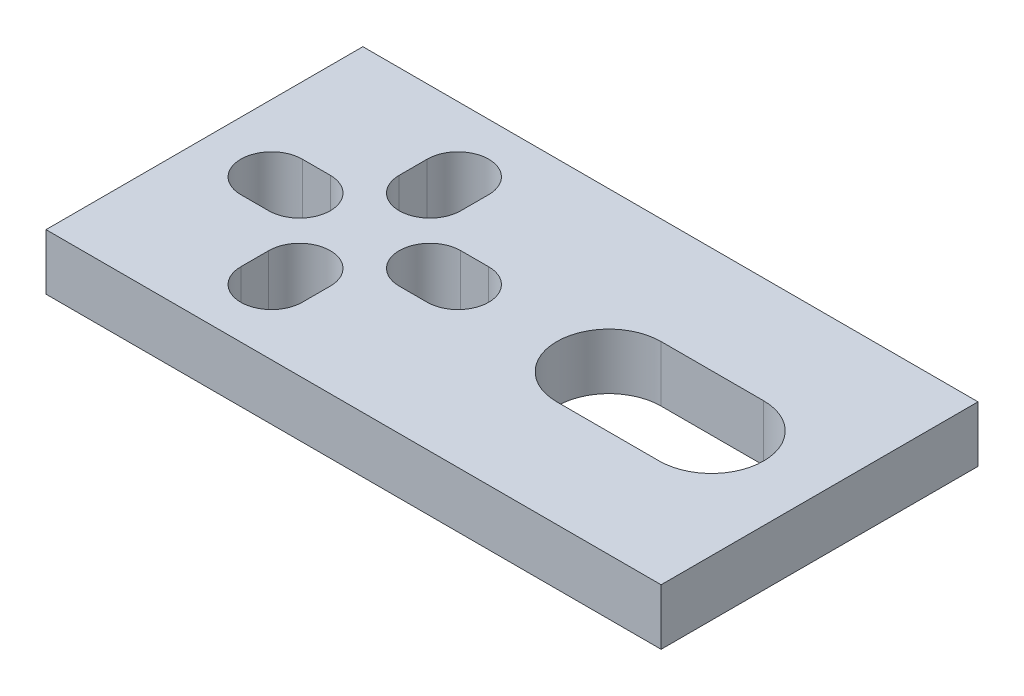
SolidWorks part; units mm, degrees
material "6061-T6 (SS)"
ref_plane "Front Plane" through (0, 0, 0) normal (0, 0, 1) x (1, 0, 0)
ref_plane "Top Plane" through (0, 0, 0) normal (0, 1, 0) x (1, 0, 0)
ref_plane "Right Plane" through (0, 0, 0) normal (1, 0, 0) x (0, 0, -1)
sketch "Sketch1" plane through (0, 0, 0) normal (0, 1, 0) x (1, 0, 0)
  line L1 (0, 0) -> (33, 0)
  line L2 (0, 0) -> (0, 17)
  line L3 (0, 17) -> (33, 17)
  line L4 (33, 0) -> (33, 17)
  dimension "D1" = 33
  dimension "D2" = 17
extrude "Boss-Extrude1" add sketch "Sketch1" along normal blind 3
sketch "Sketch2" plane through (0, 3, 0) normal (0, 1, 0) x (1, 0, 0)
  line L0 (0, 8.5) -> (33, 8.5) construction
  line L1 (0, 17) -> (0, 0) construction
  line L2 (33, 0) -> (33, 17) construction
  line L3 (8.6, 8.5) -> (8.6, 12.75) construction
  line L4 (21.7, 8.5) -> (27.2, 8.5) construction
  line L5 (21.7, 11.3) -> (27.2, 11.3)
  line L6 (21.7, 5.7) -> (27.2, 5.7)
  line L7 (8.6, 12) -> (8.6, 13.5) construction
  line L8 (6.95, 12) -> (6.95, 13.5)
  line L9 (10.25, 12) -> (10.25, 13.5)
  line L10 (3.6, 8.5) -> (5.1, 8.5) construction
  line L11 (3.6, 10.15) -> (5.1, 10.15)
  line L12 (3.6, 6.85) -> (5.1, 6.85)
  line L13 (13.6, 8.5) -> (12.1, 8.5) construction
  line L14 (13.6, 10.15) -> (12.1, 10.15)
  line L15 (13.6, 6.85) -> (12.1, 6.85)
  line L16 (8.6, 5) -> (8.6, 3.5) construction
  line L17 (6.95, 5) -> (6.95, 3.5)
  line L18 (10.25, 5) -> (10.25, 3.5)
  arc A0 (21.7, 11.3) -> (21.7, 5.7) centre (21.7, 8.5) ccw
  arc A1 (27.2, 5.7) -> (27.2, 11.3) centre (27.2, 8.5) ccw
  arc A2 (6.95, 12) -> (10.25, 12) centre (8.6, 12) ccw
  arc A3 (10.25, 13.5) -> (6.95, 13.5) centre (8.6, 13.5) ccw
  arc A4 (3.6, 10.15) -> (3.6, 6.85) centre (3.6, 8.5) ccw
  arc A5 (5.1, 6.85) -> (5.1, 10.15) centre (5.1, 8.5) ccw
  arc A6 (13.6, 10.15) -> (13.6, 6.85) centre (13.6, 8.5) cw
  arc A7 (12.1, 6.85) -> (12.1, 10.15) centre (12.1, 8.5) cw
  arc A8 (6.95, 5) -> (10.25, 5) centre (8.6, 5) cw
  arc A9 (10.25, 3.5) -> (6.95, 3.5) centre (8.6, 3.5) cw
  point P10 (24.45, 8.5)
  point P17 (8.6, 12.75)
  point P24 (4.35, 8.5)
  point P31 (12.85, 8.5)
  point P38 (8.6, 4.25)
  dimension "D1" = 5.6
  dimension "D2" = 5.5
  dimension "D3" = 3.3
  dimension "D4" = 1.5
  dimension "D5" = 10
  dimension "D6" = 10
  dimension "D7" = 3.6
  dimension "D8" = 3
extrude "Cut-Extrude1" cut sketch "Sketch2" against normal through all
